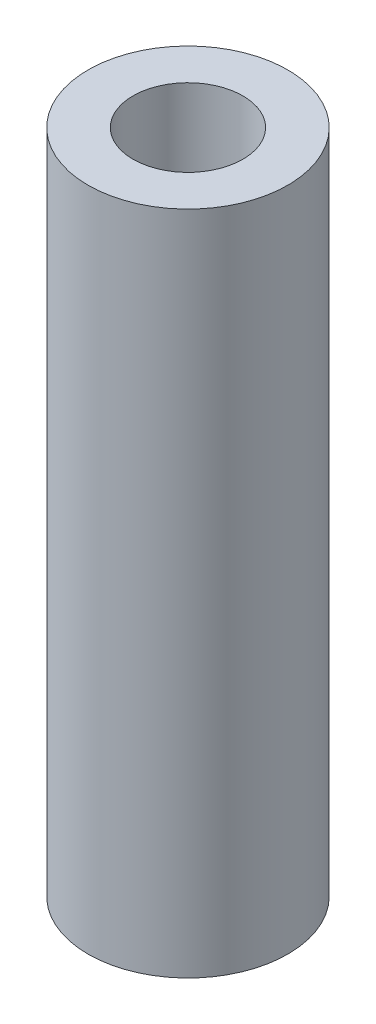
SolidWorks part; units mm, degrees
ref_plane "Front Plane" through (0, 0, 0) normal (0, 0, 1) x (1, 0, 0)
ref_plane "Top Plane" through (0, 0, 0) normal (0, 1, 0) x (1, 0, 0)
ref_plane "Right Plane" through (0, 0, 0) normal (1, 0, 0) x (0, 0, -1)
sketch "Sketch1" plane through (0, 0, 0) normal (0, 1, 0) x (1, 0, 0)
  circle A0 centre (0, 0) radius 3
  circle A1 centre (0, 0) radius 1.65
  dimension "D1" = 3.3
  dimension "D2" = 6
extrude "Boss-Extrude1" add sketch "Sketch1" along normal blind 20
